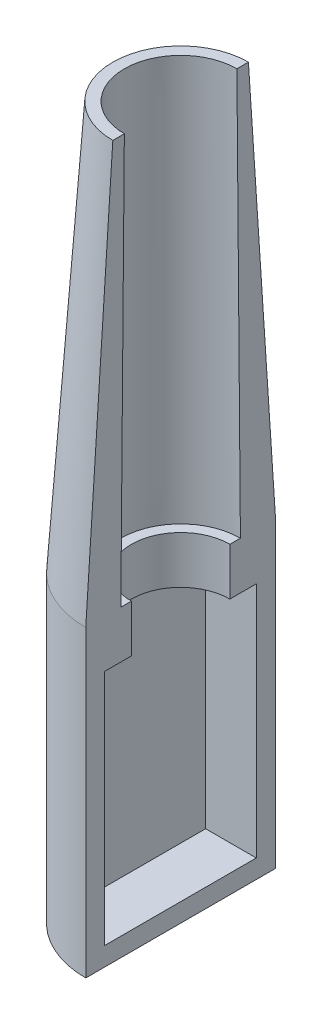
SolidWorks part; units mm, degrees
ref_plane "Front Plane" through (0, 0, 0) normal (0, 0, 1) x (1, 0, 0)
ref_plane "Top Plane" through (0, 0, 0) normal (0, 1, 0) x (1, 0, 0)
ref_plane "Right Plane" through (0, 0, 0) normal (1, 0, 0) x (0, 0, -1)
sketch "Sketch2" plane through (0, 0, 0) normal (0, 1, 0) x (1, 0, 0)
  circle A0 centre (0, 0) radius 25.4
extrude "Boss-Extrude1" add sketch "Sketch2" along normal blind 63.5 and the other way blind 17.78 contours A0
sketch "Sketch3" plane through (0, 63.5, 0) normal (0, 1, 0) x (1, 0, 0)
  circle A0 centre (0, 0) radius 25.4
extrude "Boss-Extrude2" add sketch "Sketch3" along normal blind 109.3175 draft 3.793
sketch "Sketch4" plane through (0, 172.8175, 0) normal (0, 1, 0) x (1, 0, 0)
  circle A0 centre (0, 0) radius 15.0686
extrude "Cut-Extrude1" cut sketch "Sketch4" against normal blind 109.3175 draft 0.493 contours A0 draft outward yes
sketch "Sketch5" plane through (0, 0, 0) normal (0, 1, 0) x (1, 0, 0)
  line L0 (0, 25.4) -> (0, -25.4)
  circle A0 centre (0, 0) radius 25.4 construction
  point P5 (0, 0)
split "Split6" trim tools "Sketch5" bodies to split 103 resulting bodies 111
sketch "Sketch7" plane through (0, 0, 0) normal (1, 0, 0) x (0, 0, -1)
  line L0 (-20.3929, 0) -> (-20.3929, 50.7918)
  line L1 (-20.3929, 50.7918) -> (20.2525, 50.7918)
  line L2 (20.2525, 50.7918) -> (20.2525, -12.7768)
  line L3 (20.2525, -12.7768) -> (-20.3929, -12.7768)
  line L4 (-20.3929, -12.7768) -> (-20.3929, 0)
extrude "Cut-Extrude3" cut sketch "Sketch7" against normal blind 13.5595
sketch "Sketch8" plane through (0, 63.5, 0) normal (0, 1, 0) x (1, 0, 0)
  line L0 (0, 16.0084) -> (0, -16.0084) construction
  circle A0 centre (0, 0) radius 13.1822
extrude "Cut-Extrude4" cut sketch "Sketch8" against normal blind 13.5595
